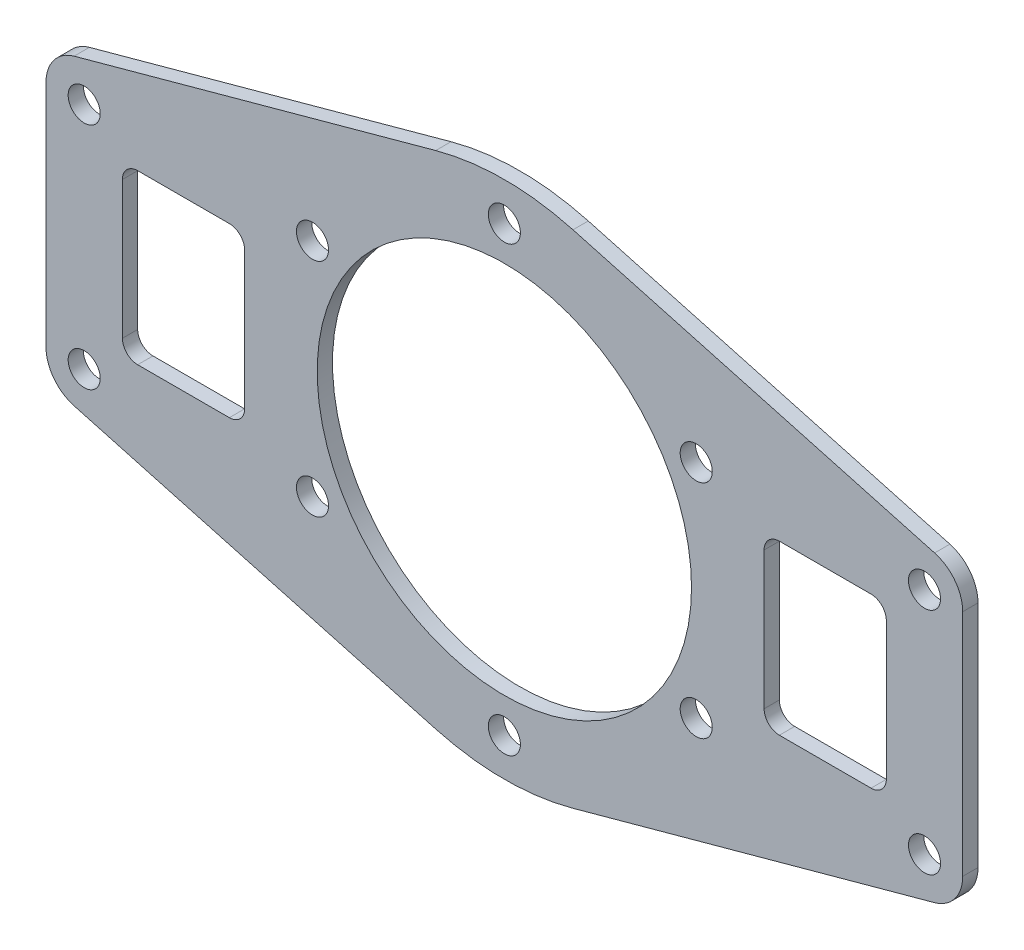
SolidWorks part; units mm, degrees
material "Thornel Mat VMA"
ref_plane "前视基准面" through (0, 0, 0) normal (0, 0, 1) x (1, 0, 0)
ref_plane "上视基准面" through (0, 0, 0) normal (0, 1, 0) x (1, 0, 0)
ref_plane "右视基准面" through (0, 0, 0) normal (1, 0, 0) x (0, 0, -1)
sketch "草图1" plane through (0, 0, 0) normal (0, 0, 1) x (1, 0, 0)
  line L0 (-60, 15) -> (-60, -15)
  line L1 (55, -15) -> (-55, -15) construction
  line L2 (55, -15) -> (55, 15) construction
  line L3 (55, 15) -> (-55, 15) construction
  line L4 (-55, -15) -> (-55, 15) construction
  line L5 (55, -15) -> (-55, 15) construction
  line L6 (55, 15) -> (-55, -15) construction
  line L7 (-56.3212, -19.8223) -> (-8.9841, -32.7915)
  line L8 (8.9841, -32.7915) -> (56.3212, -19.8223)
  line L9 (60, -15) -> (60, 15)
  line L10 (56.3212, 19.8223) -> (8.9841, 32.7915)
  line L11 (-8.9841, 32.7915) -> (-56.3212, 19.8223)
  circle A0 centre (0, 0) radius 24.5
  circle A1 centre (0, 0) radius 29 construction
  circle A2 centre (0, 29) radius 2.1
  circle A3 centre (25.1147, 14.5) radius 2.1
  circle A4 centre (25.1147, -14.5) radius 2.1
  circle A5 centre (0, -29) radius 2.1
  circle A6 centre (-25.1147, -14.5) radius 2.1
  circle A7 centre (-25.1147, 14.5) radius 2.1
  circle A8 centre (-55, 15) radius 2.1
  circle A9 centre (-55, -15) radius 2.1
  circle A10 centre (55, -15) radius 2.1
  circle A11 centre (55, 15) radius 2.1
  arc A12 (-8.9841, -32.7915) -> (8.9841, -32.7915) centre (0, 0) ccw
  arc A13 (8.9841, 32.7915) -> (-8.9841, 32.7915) centre (0, 0) ccw
  arc A14 (60, 15) -> (56.3212, 19.8223) centre (55, 15) ccw
  arc A15 (56.3212, -19.8223) -> (60, -15) centre (55, -15) ccw
  arc A16 (-60, -15) -> (-56.3212, -19.8223) centre (-55, -15) ccw
  arc A17 (-60, 15) -> (-56.3212, 19.8223) centre (-55, 15) cw
  point P18 (0, 0)
  dimension "D1" = 49
  dimension "D2" = 58
  dimension "D3" = 4.2
  dimension "D5" = 4.2
  dimension "D8" = 34
  dimension "D9" = 5
  dimension "D6" = 30
  dimension "D7" = 110
  dimension "D4" = 6
extrude "凸台-拉伸1" add sketch "草图1" along normal blind 2
sketch "草图2" plane through (0, 0, 2) normal (0, 0, 1) x (1, 0, 0)
  line L0 (34, 0) -> (-34, 0) construction
  line L1 (-48, 11) -> (-36, 11)
  line L2 (-50, 9) -> (-50, -9)
  line L3 (-48, -11) -> (-36, -11)
  line L4 (-34, 9) -> (-34, -9)
  line L5 (36, 11) -> (48, 11)
  line L6 (34, 9) -> (34, -9)
  line L7 (36, -11) -> (48, -11)
  line L8 (50, 9) -> (50, -9)
  line L9 (-60, 15) -> (-60, -15) construction
  arc A0 (48, 11) -> (50, 9) centre (48, 9) cw
  arc A1 (34, -9) -> (36, -11) centre (36, -9) ccw
  arc A2 (48, -11) -> (50, -9) centre (48, -9) ccw
  arc A3 (36, 11) -> (34, 9) centre (36, 9) ccw
  arc A4 (-36, 11) -> (-34, 9) centre (-36, 9) cw
  arc A5 (-50, -9) -> (-48, -11) centre (-48, -9) ccw
  arc A6 (-36, -11) -> (-34, -9) centre (-36, -9) ccw
  arc A7 (-48, 11) -> (-50, 9) centre (-48, 9) ccw
  point P25 (-50, -11)
  point P30 (-50, 11)
  dimension "D4" = 2
  dimension "D5" = 2
  dimension "D1" = 68
  dimension "D2" = 10
  dimension "D3" = 22
extrude "切除-拉伸1" cut sketch "草图2" against normal blind 10
